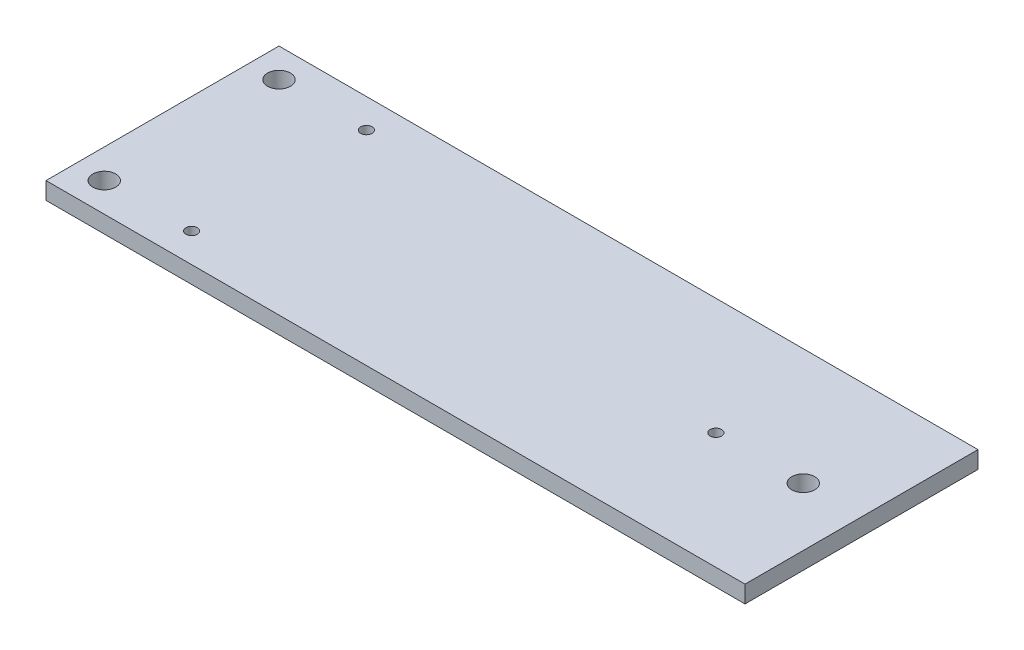
SolidWorks part; units mm, degrees
ref_plane "Front Plane" through (0, 0, 0) normal (0, 0, 1) x (1, 0, 0)
ref_plane "Top Plane" through (0, 0, 0) normal (0, 1, 0) x (1, 0, 0)
ref_plane "Right Plane" through (0, 0, 0) normal (1, 0, 0) x (0, 0, -1)
sketch "Sketch1" plane through (0, 0, 0) normal (0, 1, 0) x (1, 0, 0)
  line L0 (0, 10.16) -> (60.96, 10.16) construction
  line L1 (0, 0) -> (60.96, 0)
  line L2 (0, 0) -> (0, 20.32)
  line L3 (0, 20.32) -> (60.96, 20.32)
  line L4 (60.96, 0) -> (60.96, 20.32)
  line L5 (30.48, 0) -> (30.48, 20.32) construction
  line L6 (2.54, 2.54) -> (21.199, 2.54) construction
  circle A0 centre (2.54, 2.54) radius 1
  circle A1 centre (55.88, 10.16) radius 1
  circle A3 centre (2.54, 17.78) radius 1
  circle A4 centre (10.16, 2.54) radius 0.5
  circle A5 centre (48.26, 10.16) radius 0.5
  circle A6 centre (10.16, 17.78) radius 0.5
  dimension "D3" = 2
  dimension "D6" = 1
  dimension "D8" = 5.08
  dimension "D1" = 60.96
  dimension "D2" = 20.32
  dimension "D4" = 2.54
  dimension "D5" = 2.54
  dimension "D7" = 7.62
  dimension "D9" = 7.62
extrude "Boss-Extrude1" add sketch "Sketch1" along normal blind 1.5
